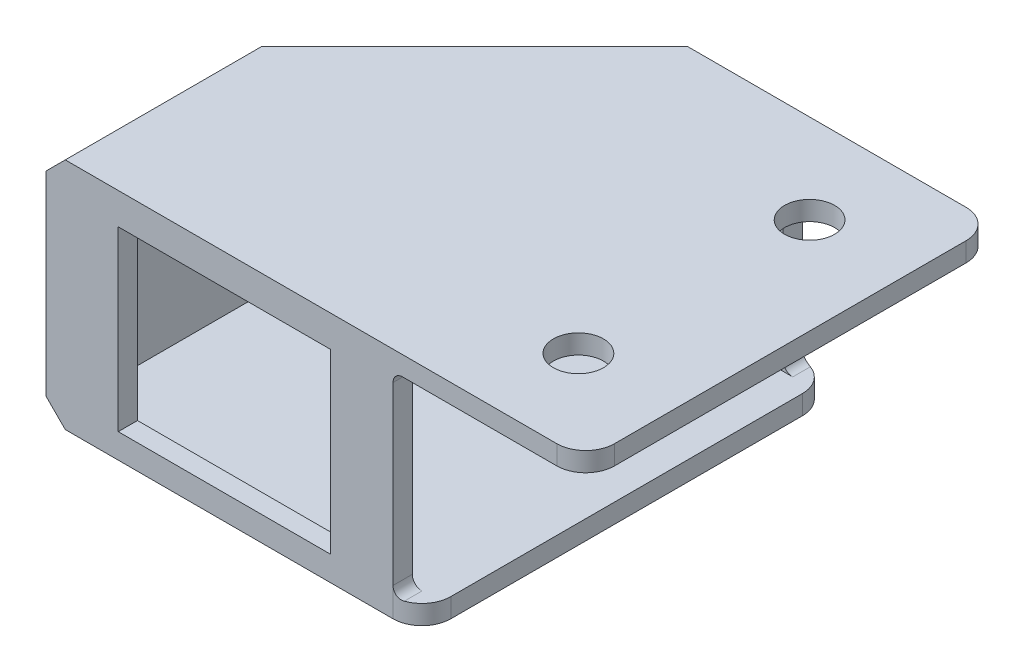
SolidWorks part; units mm, degrees
ref_plane "Front Plane" through (0, 0, 0) normal (0, 0, 1) x (1, 0, 0)
ref_plane "Top Plane" through (0, 0, 0) normal (0, 1, 0) x (1, 0, 0)
ref_plane "Right Plane" through (0, 0, 0) normal (1, 0, 0) x (0, 0, -1)
sketch "Sketch1" plane through (0, 0, 0) normal (0, 0, 1) x (1, 0, 0)
  line L0 (-2.1203, 12.6097) -> (18.9097, 12.6097)
  line L1 (18.9097, 12.6097) -> (18.9097, -5.8103)
  line L2 (24.4097, 13.3997) -> (24.4097, -6.3503)
  line L3 (26.4097, 13.8997) -> (26.4097, -6.3503)
  line L4 (29.4097, -6.3503) -> (29.4097, -8.3503)
  line L5 (46.4097, 15.8997) -> (46.4097, 13.8997)
  line L6 (18.9097, -5.8103) -> (-2.1203, -5.8103)
  line L7 (-2.1203, 12.6097) -> (-2.1203, -5.8103)
  line L8 (-7.6203, 13.3997) -> (-7.6203, -6.3503)
  line L9 (-9.6203, 15.8997) -> (-9.6203, -8.3503)
  line L11 (26.4097, -6.3503) -> (29.4097, -6.3503)
  line L12 (-9.6203, -8.3503) -> (29.4097, -8.3503)
  line L14 (26.4097, 13.8997) -> (46.4097, 13.8997)
  line L15 (-9.6203, 15.8997) -> (46.4097, 15.8997)
  line L16 (-7.6203, 13.8997) -> (24.4097, 13.8997)
  line L17 (24.4097, 13.8997) -> (24.4097, 13.8997)
  line L18 (24.4097, 13.8997) -> (24.4097, 13.8997)
  line L19 (24.4097, 13.8997) -> (24.4097, -6.3503)
  line L20 (24.4097, -6.3503) -> (24.4097, -6.3503)
  line L21 (24.4097, -6.3503) -> (24.4097, -6.3503)
  line L22 (-7.6203, -6.3503) -> (24.4097, -6.3503)
  line L23 (-7.6203, 13.8997) -> (-7.6203, -6.3503)
  dimension "D1" = 20.25
  dimension "D2" = 2
  dimension "D3" = 2
  dimension "D4" = 2
extrude "Boss-Extrude1" add sketch "Sketch1" along normal blind 42.5
sketch "Sketch2" plane through (0, 0, 42.5) normal (0, 0, 1) x (1, 0, 0)
  line L0 (-7.6203, 13.8997) -> (24.4097, 13.8997)
  line L1 (-7.6203, 13.8997) -> (-7.6203, -6.3503)
  line L2 (-7.6203, -6.3503) -> (24.4097, -6.3503)
  line L3 (24.4097, -6.3503) -> (24.4097, 13.8997)
  line L4 (-7.6203, 3.3997) -> (24.4097, 3.3997) construction
  line L5 (8.3947, -6.6003) -> (8.3947, 13.3997) construction
  line L6 (-2.1203, -5.7874) -> (19.9097, -5.7874)
  line L7 (19.9097, -5.7874) -> (19.9097, 12.6326)
  line L8 (19.9097, 12.6326) -> (-2.1203, 12.6326)
  line L9 (-2.1203, 12.6326) -> (-2.1203, -5.7874)
  dimension "D1" = 22.03
  dimension "D2" = 18.42
extrude "Boss-Extrude2" add sketch "Sketch2" against normal blind 2
sketch "Sketch3" plane through (0, -8.3503, 0) normal (0, -1, 0) x (1, 0, 0)
  line L0 (-9.6203, 0) -> (-9.6203, 21.25)
  line L1 (-9.6203, 42.5) -> (-9.6203, 0) construction
  line L2 (-9.6203, 0) -> (11.6297, 0)
  line L4 (-9.6203, 0) -> (29.4097, 0) construction
  line L5 (-9.6203, 21.25) -> (11.6297, 0)
extrude "Cut-Extrude1" cut sketch "Sketch3" against normal through all
fillet "Fillet1" radius 3 4 edges at (46.4097, 14.8997, 0) (29.4097, -7.3503, 0) (46.4097, 14.8997, 42.5) (29.4097, -7.3503, 42.5)
sketch "Sketch6" plane through (0, 15.8997, 0) normal (0, 1, 0) x (1, 0, 0)
  line L0 (46.4097, -39.5) -> (46.4097, -3)
  line L1 (46.4097, -39.5) -> (46.4097, -3) construction
  line L2 (36.4097, -39.5) -> (36.4097, -3) construction
  line L3 (43.4097, -42.5) -> (31.7173, -42.5)
  line L4 (-9.6203, -42.5) -> (43.4097, -42.5) construction
  line L5 (36.4097, -21.25) -> (46.4097, -21.25) construction
  arc A0 (46.4097, -3) -> (43.4097, 0) centre (43.4097, -3) ccw construction
  circle A1 centre (36.4097, -33.25) radius 2.6
  circle A2 centre (36.4097, -9.25) radius 2.6
  dimension "D3" = 5.2
  dimension "D1" = 12
extrude "Cut-Extrude3" cut sketch "Sketch6" against normal through all contours A1 | A2
chamfer "Chamfer2" distance 2 angle 45 4 edges at (1.0047, 15.8997, 10.625) (-9.6203, 15.8997, 31.875) (1.0047, -8.3503, 10.625) (-9.6203, -8.3503, 31.875)
sketch "Sketch7" plane through (0, -6.3503, 0) normal (0, 1, 0) x (1, 0, 0)
  line L0 (24.4097, 0) -> (11.6297, 0)
  line L1 (11.6297, 0) -> (24.4097, 0) construction
  line L2 (11.6297, 0) -> (-7.6203, -19.25)
  line L3 (24.4097, -2) -> (12.4582, -2)
  line L4 (12.4582, -2) -> (-7.6203, -22.0784)
  line L5 (24.4097, -2) -> (24.4097, 0)
  line L6 (-7.6203, -19.25) -> (-7.6203, -22.0784)
  line L8 (12.4582, -2) -> (-6.206, -20.6642) construction
  dimension "D1" = 2
extrude "Boss-Extrude3" add sketch "Sketch7" along normal up to next
sketch "Sketch8" plane through (26.4097, 0, 0) normal (1, 0, 0) x (0, 0, -1)
  line L1 (-40.5, -6.3503) -> (-2, -6.3503)
  line L2 (-42.5, -6.3503) -> (0, -6.3503) construction
  line L3 (-2, 13.8997) -> (-42.5, 13.8997)
  line L4 (-40.5, 13.8997) -> (-40.5, -6.3503)
  line L5 (-40.5, 11.8997) -> (-40.5, -4.3503) construction
  line L6 (-2, -6.3503) -> (-2, 13.8997)
  line L7 (-2, -4.3503) -> (-2, 11.8997) construction
  line L8 (-40.5, -4.3503) -> (-2, -4.3503) construction
  line L9 (-2, 11.8997) -> (-40.5, 11.8997) construction
  line L10 (-42.5, 13.8997) -> (-42.5, -6.3503) construction
  line L11 (0, -6.3503) -> (0, 13.8997) construction
  line L12 (0, 13.8997) -> (-42.5, 13.8997) construction
  line M2 (0, 13.8997) -> (-42.5, 13.8997)
  line M4 (-42.5, -6.3503) -> (0, -6.3503)
  dimension "D1" = 2
extrude "Cut-Extrude4" cut sketch "Sketch8" against normal up to next contours L6 L4 M4 M2
fillet "Fillet2" radius 1 4 edges at (26.4097, 13.8997, 1) (26.4097, 13.8997, 41.5) (26.4097, -6.3503, 41.5) (26.4097, -6.3503, 1)
